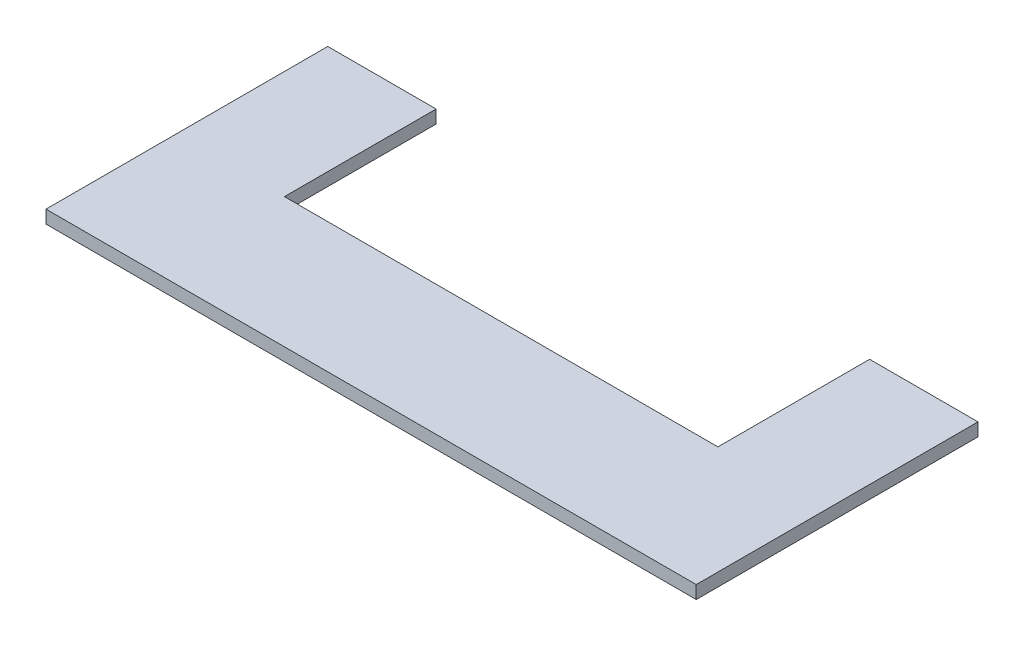
SolidWorks part; units mm, degrees
material "Plain Carbon Steel"
ref_plane "Front Plane" through (0, 0, 0) normal (0, 0, 1) x (1, 0, 0)
ref_plane "Top Plane" through (0, 0, 0) normal (0, 1, 0) x (1, 0, 0)
ref_plane "Right Plane" through (0, 0, 0) normal (1, 0, 0) x (0, 0, -1)
sketch "Sketch1" plane through (0, 0, 0) normal (0, 1, 0) x (1, 0, 0)
  line L0 (100, 65) -> (150, 65)
  line L1 (-150, -65) -> (150, -65)
  line L2 (-150, -65) -> (-150, 65)
  line L3 (-150, 65) -> (-100, 65)
  line L4 (150, -65) -> (150, 65)
  line L5 (-150, -65) -> (150, 65) construction
  line L6 (-150, 65) -> (150, -65) construction
  line L8 (100, 65) -> (100, -5)
  line L9 (100, -5) -> (-100, -5)
  line L10 (-100, 65) -> (-100, -5)
  point P0 (0, 0)
  dimension "D1" = 130
  dimension "D2" = 300
  dimension "D3" = 70
  dimension "D4" = 200
  dimension "D5" = 50
extrude "Boss-Extrude1" add sketch "Sketch1" along normal blind 6
sketch "Sketch2" [suppressed] plane through (0, 6, 0) normal (0, 1, 0) x (1, 0, 0)
  line L0 (150, -65) -> (150, 65) construction
  line L1 (-150, -65) -> (150, -65) construction
  circle A0 centre (125, 4) radius 13.5
  dimension "D1" = 27
  dimension "D2" = 25
  dimension "D3" = 69
extrude "Cut-Extrude1" [suppressed] cut sketch "Sketch2" against normal through all
